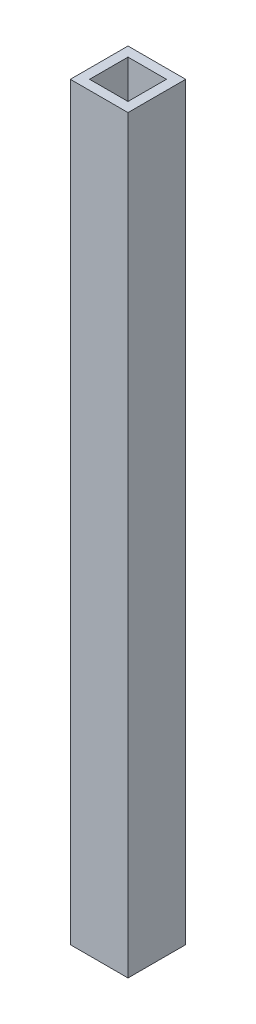
SolidWorks part; units mm, degrees
ref_plane "Front" through (0, 0, 0) normal (0, 0, 1) x (1, 0, 0)
ref_plane "Top" through (0, 0, 0) normal (0, 1, 0) x (1, 0, 0)
ref_plane "Right" through (0, 0, 0) normal (1, 0, 0) x (0, 0, -1)
sketch "Sketch1" plane through (0, 0, 0) normal (0, 1, 0) x (1, 0, 0)
  line L1 (0, 0) -> (30, 0)
  line L2 (0, 0) -> (0, 30)
  line L3 (0, 30) -> (30, 30)
  line L4 (30, 0) -> (30, 30)
  line L5 (5, 25) -> (25, 25)
  line L6 (5, 25) -> (5, 5)
  line L7 (5, 5) -> (25, 5)
  line L8 (25, 25) -> (25, 5)
  dimension "D1" = 30
  dimension "D2" = 30
  dimension "D3" = 5
  dimension "D4" = 5
  dimension "D5" = 5
  dimension "D6" = 5
extrude "Boss-Extrude1" add sketch "Sketch1" along normal blind 390
